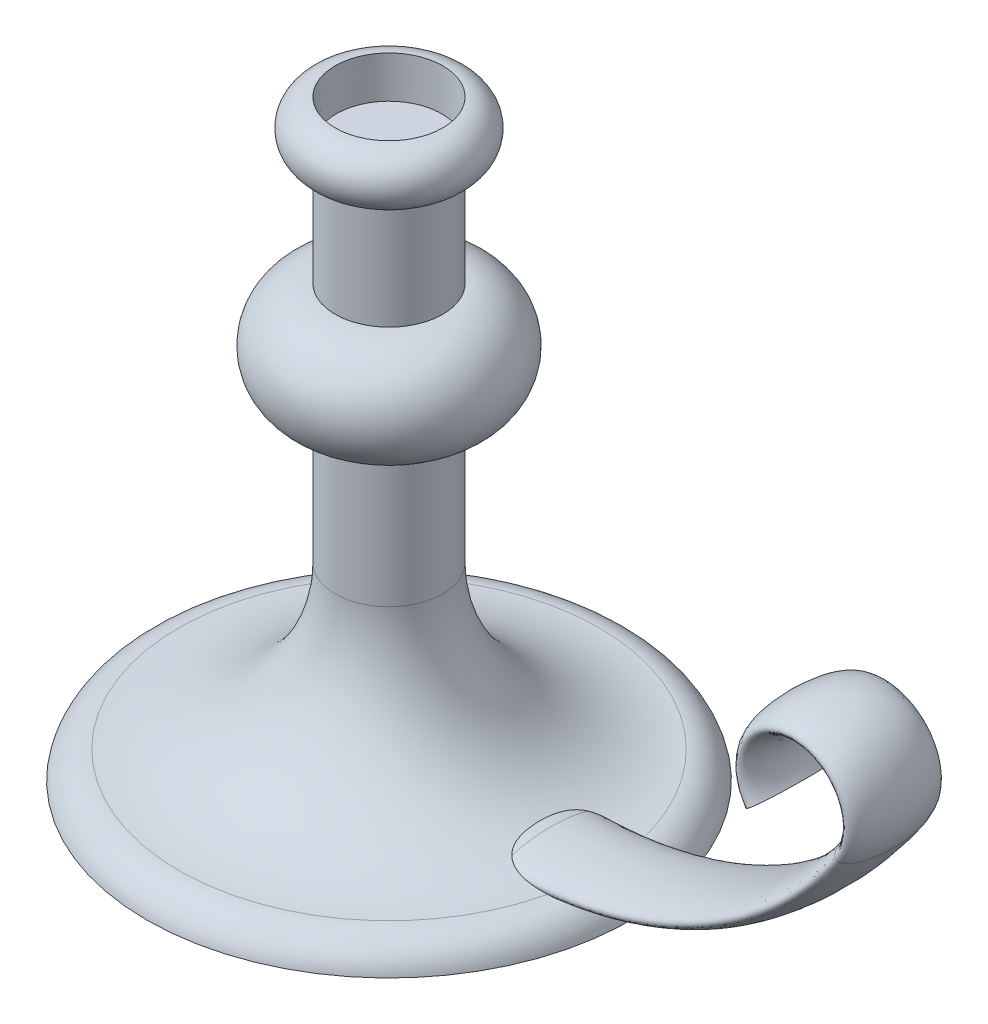
SolidWorks part; units mm, degrees
ref_plane "Front Plane" through (0, 0, 0) normal (0, 0, 1) x (1, 0, 0)
ref_plane "Top Plane" through (0, 0, 0) normal (0, 1, 0) x (1, 0, 0)
ref_plane "Right Plane" through (0, 0, 0) normal (1, 0, 0) x (0, 0, -1)
sketch "Sketch1" plane through (0, 0, 0) normal (0, 0, 1) x (1, 0, 0)
  line L0 (0, 0) -> (0, 5588)
  line L1 (0, 0) -> (2286, 0)
  line L2 (0, 5588) -> (508, 5588)
  line L3 (508, 5080) -> (508, 4064)
  line L4 (508, 3048) -> (508, 1778)
  arc A0 (508, 5588) -> (508, 5080) centre (508, 5334) cw
  arc A1 (508, 4064) -> (508, 3048) centre (508, 3556) cw
  arc A2 (508, 1778) -> (1984.6077, 254.7371) centre (2032, 1778) ccw
  arc A3 (1984.6077, 254.7371) -> (2286, 0) centre (1974.7343, -62.6094) cw
  dimension "D6" = 508
  dimension "D10" = 317.5
  dimension "D11" = 1524
  dimension "D1" = 5588
  dimension "D2" = 2286
  dimension "D3" = 508
  dimension "D4" = 254
  dimension "D5" = 1270
  dimension "D7" = 1016
  dimension "D8" = 3810
  dimension "D9" = 1778
revolve "Revolve1" add sketch "Sketch1" angle 360 about L0
sketch "Sketch2" plane through (0, 0, 0) normal (0, 0, 1) x (1, 0, 0)
  line L0 (0, 254) -> (1524, 254)
  line L3 (0, 5776.8641) -> (0, 4448.2717) construction
  line L4 (0, 5080) -> (0, 4064) construction
  arc A0 (1524, 254) -> (4663.2386, 1905) centre (1524, 4064) ccw
  arc A1 (4663.2386, 1905) -> (3826.1083, 1905) centre (4244.6735, 2192.8667) ccw
  dimension "D3" = 3810
  dimension "D4" = 508
  dimension "D1" = 1524
  dimension "D2" = 1651
  dimension "D5" = 254
sketch "Sketch5" plane through (0, 0, 0) normal (1, 0, 0) x (0, 0, -1)
  ellipse E0 centre (0, 254) end of major axis (444.5, 254) minor radius 127
  dimension "D1" = 889
  dimension "D2" = 254
sweep "Sweep1" add profiles "Sketch5" path "Sketch2"
sketch "Sketch7" plane through (0, 5588, 0) normal (0, 1, 0) x (1, 0, 0)
  circle A0 centre (0, 0) radius 508
extrude "Cut-Extrude1" cut sketch "Sketch7" against normal blind 387.604 draft 1.5
